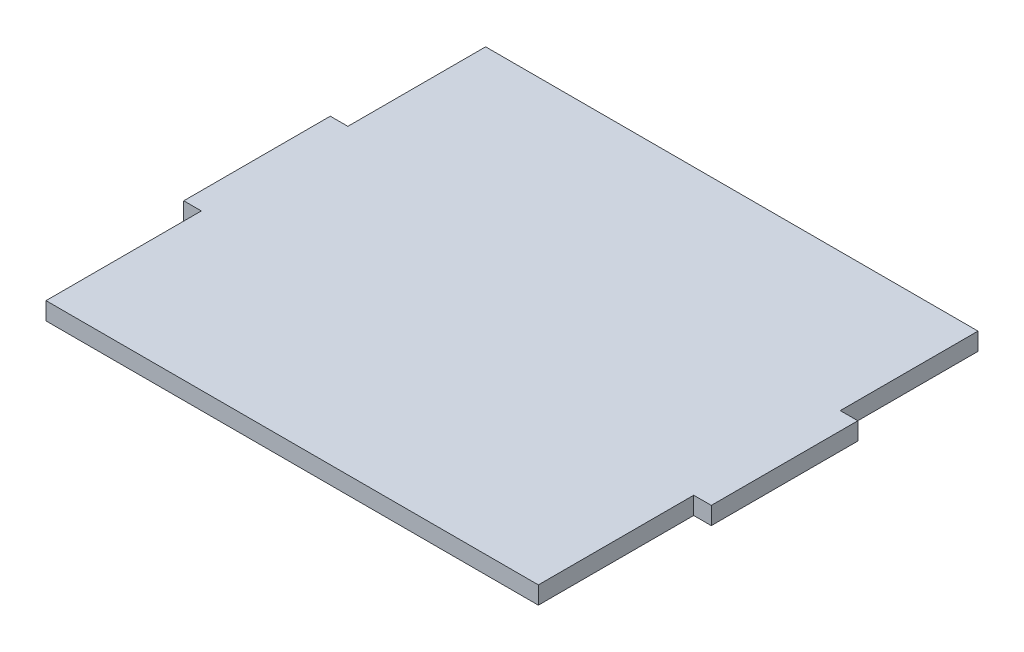
SolidWorks part; units mm, degrees
ref_plane "Front Plane" through (0, 0, 0) normal (0, 0, 1) x (1, 0, 0)
ref_plane "Top Plane" through (0, 0, 0) normal (0, 1, 0) x (1, 0, 0)
ref_plane "Right Plane" through (0, 0, 0) normal (1, 0, 0) x (0, 0, -1)
sketch "Sketch1" plane through (0, 0, 0) normal (0, 1, 0) x (1, 0, 0)
  line L1 (0, 0) -> (76.2, 0)
  line L2 (0, 0) -> (0, 63.5)
  line L3 (0, 63.5) -> (76.2, 63.5)
  line L4 (76.2, 0) -> (76.2, 63.5)
  dimension "D1" = 76.2
  dimension "D2" = 63.5
extrude "Boss-Extrude1" add sketch "Sketch1" along normal blind 2.54 contours L4 L3 L2 L1
sketch "Sketch2" plane through (0, 2.54, 0) normal (0, 1, 0) x (1, 0, 0)
  line L1 (0, 63.5) -> (2.54, 63.5)
  line L2 (0, 63.5) -> (0, 43.6033)
  line L3 (0, 43.6033) -> (2.54, 43.6033)
  line L4 (2.54, 63.5) -> (2.54, 43.6033)
  dimension "D1" = 19.8967
  dimension "D2" = 2.54
extrude "Cut-Extrude1" cut sketch "Sketch2" against normal through all contours L2 L1 L4 L3
sketch "Sketch3" plane through (0, 2.54, 0) normal (0, 1, 0) x (1, 0, 0)
  line L1 (0, 0) -> (2.54, 0)
  line L2 (0, 0) -> (0, 22.4367)
  line L3 (0, 22.4367) -> (2.54, 22.4367)
  line L4 (2.54, 0) -> (2.54, 22.4367)
  line L5 (76.2, 63.5) -> (73.66, 63.5)
  line L6 (76.2, 63.5) -> (76.2, 43.6033)
  line L7 (76.2, 43.6033) -> (73.66, 43.6033)
  line L8 (73.66, 63.5) -> (73.66, 43.6033)
  line L9 (76.2, 0) -> (73.66, 0)
  line L10 (76.2, 0) -> (76.2, 22.4367)
  line L11 (76.2, 22.4367) -> (73.66, 22.4367)
  line L12 (73.66, 0) -> (73.66, 22.4367)
  dimension "D1" = 2.54
  dimension "D2" = 22.4367
  dimension "D3" = 22.4367
  dimension "D4" = 2.54
  dimension "D5" = 19.8967
  dimension "D6" = 2.54
extrude "Cut-Extrude2" cut sketch "Sketch3" against normal through all contours L2 L1 L4 L3 | L10 L9 L12 L11 | L6 L5 L8 L7
equation "\"Matterial_Thickness\"= \"GMaterial\""
equation "\"D2@Sketch2\"=\"Matterial_Thickness\""
equation "\"D1@Sketch3\"=\"Matterial_Thickness\""
equation "\"D6@Sketch3\"=\"Matterial_Thickness\""
equation "\"D4@Sketch3\"=\"Matterial_Thickness\""
equation "\"D1@Boss-Extrude1\"=\"Matterial_Thickness\""
equation "\"GMaterial\"= \"Foamcore\""
equation "\"MDF\" = 0.3in"
equation "\"Foamcore\"= 0.1in"
